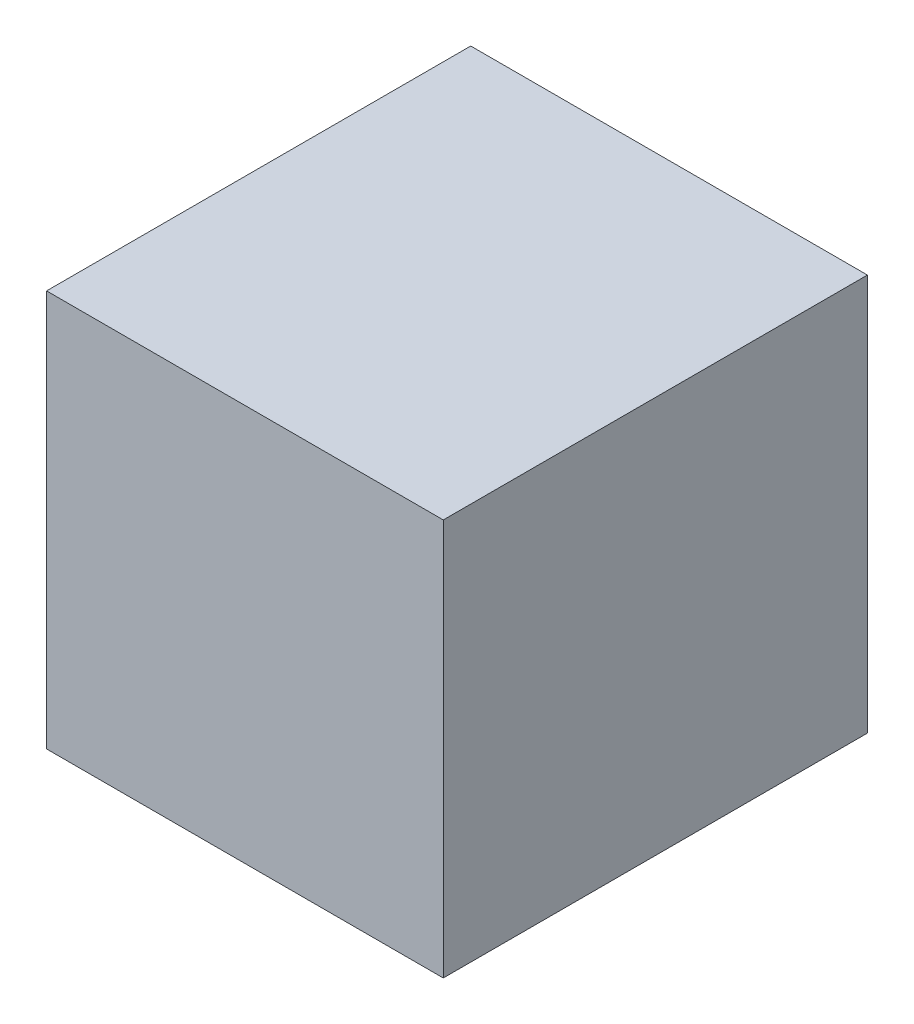
SolidWorks part; units mm, degrees
ref_plane "Front Plane" through (0, 0, 0) normal (0, 0, 1) x (1, 0, 0)
ref_plane "Top Plane" through (0, 0, 0) normal (0, 1, 0) x (1, 0, 0)
ref_plane "Right Plane" through (0, 0, 0) normal (1, 0, 0) x (0, 0, -1)
sketch "Sketch1" plane through (0, 0, 0) normal (0, 0, 1) x (1, 0, 0)
  line L0 (15.9, 0) -> (-15.9, 0) construction
  line L1 (-15.9, -12.2) -> (15.9, -12.2)
  line L2 (-15.9, -12.2) -> (-15.9, 19.6)
  line L3 (-15.9, 19.6) -> (15.9, 19.6)
  line L4 (15.9, -12.2) -> (15.9, 19.6)
  line L5 (-15.9, -12.2) -> (15.9, 19.6) construction
  line L6 (-15.9, 19.6) -> (15.9, -12.2) construction
  point P0 (0, 3.7)
  point P5 (0, 0)
  dimension "D1" = 31.8
  dimension "D2" = 31.8
  dimension "D3" = 12.2
ref_plane "Plane4" through (0, 0, -2) normal (0, 0, 1) x (1, 0, 0)
extrude "Boss-Extrude1" add sketch "Sketch1" against normal blind 36
other "SurfaceCut1"
